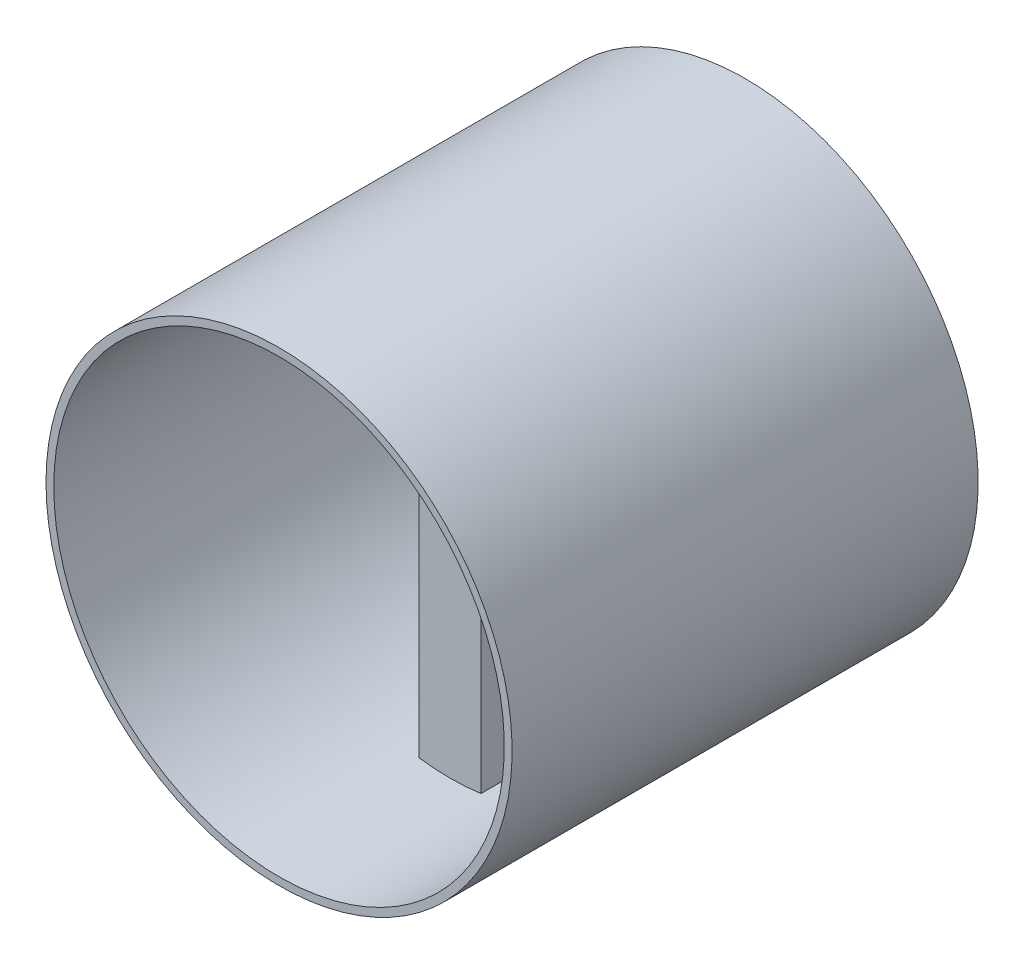
SolidWorks part; units mm, degrees
ref_plane "Plan de face" through (0, 0, 0) normal (0, 0, 1) x (1, 0, 0)
ref_plane "Plan de dessus" through (0, 0, 0) normal (0, 1, 0) x (1, 0, 0)
ref_plane "Plan de droite" through (0, 0, 0) normal (1, 0, 0) x (0, 0, -1)
sketch "Esquisse1" plane through (0, 0, 0) normal (0, 0, 1) x (1, 0, 0)
  line L1 (0, 0) -> (8, 0)
  line L2 (0, 0) -> (0, 59)
  line L3 (0, 59) -> (8, 59)
  line L4 (8, 0) -> (8, 59)
  dimension "D1" = 59
  dimension "D2" = 8
extrude "Boss.-Extru.1" add sketch "Esquisse1" along normal blind 60
sketch "Esquisse3" plane through (0, 0, 0) normal (0, 0, -1) x (-1, 0, 0)
  line L0 (-4, 59) -> (-4, 0) construction
  line L1 (-8, 59) -> (0, 59) construction
  line L2 (0, 0) -> (-8, 0) construction
  line L3 (0, 29.5) -> (-8, 29.5) construction
  line L4 (0, 59) -> (0, 0) construction
  line L5 (-8, 0) -> (-8, 59) construction
  circle A0 centre (-4, 29.5) radius 30
  circle A1 centre (-4, 29.5) radius 29
  dimension "D1" = 60
  dimension "D2" = 58
extrude "Boss.-Extru.2" add sketch "Esquisse3" against normal blind 60
sketch "Esquisse4" plane through (0, 0, 0) normal (0, 0, -1) x (-1, 0, 0)
  line L0 (-4, -0.5) -> (-4, 59.5) construction
  line L1 (-43.5151, 29.5) -> (32.2355, 29.5) construction
  circle A0 centre (-4, 29.5) radius 30 construction
  circle A5 centre (-4, 29.5) radius 29
  dimension "D1" = 58
extrude "Enlèv. mat.-Extru.3" cut sketch "Esquisse4" against normal blind 30
sketch "Esquisse5" plane through (0, 0, 30) normal (0, 0, -1) x (-1, 0, 0)
  line L0 (-4, 58.5) -> (-4, 0.5) construction
  line L1 (25, 29.5) -> (-33, 29.5) construction
  line L3 (-6, 43) -> (-6.9673, 29.942)
  line L5 (-6, 16) -> (-6.9673, 29.058)
  line L6 (-1.0327, 29.942) -> (-2, 43)
  line L7 (-2, 16) -> (-1.0327, 29.058)
  arc A0 (0, 58.2228) -> (-8, 58.2228) centre (-4, 29.5) ccw construction
  arc A1 (-8, 0.7772) -> (0, 0.7772) centre (-4, 29.5) ccw construction
  circle A2 centre (-4, 29.5) radius 29 construction
  arc A3 (-6.9673, 29.942) -> (-6.9673, 29.058) centre (-4, 29.5) ccw
  arc A4 (-2, 43) -> (-6, 43) centre (-4, 43) ccw
  arc A5 (-2, 16) -> (-6, 16) centre (-4, 16) cw
  arc A7 (-1.0327, 29.942) -> (-1.0327, 29.058) centre (-4, 29.5) cw
  dimension "D1" = 6
  dimension "D2" = 4
  dimension "D3" = 13.5
  dimension "D4" = 13.058
  dimension "D5" = 13.058
  dimension "D6" = 171.527
extrude "Enlèv. mat.-Extru.5" cut sketch "Esquisse5" against normal blind 1.5
sketch "Esquisse6" plane through (0, 0, 60) normal (0, 0, 1) x (1, 0, 0)
  line L0 (4, 59.5) -> (4, -0.5) construction
  line L1 (-25, 29.5) -> (33, 29.5) construction
  circle A0 centre (4, 29.5) radius 30 construction
  arc A1 (0, 58.2228) -> (0, 0.7772) centre (4, 29.5) ccw construction
  arc A2 (8, 0.7772) -> (8, 58.2228) centre (4, 29.5) ccw construction
  circle A3 centre (4, 29.5) radius 29
  dimension "D1" = 58
extrude "Enlèv. mat.-Extru.6" cut sketch "Esquisse6" against normal blind 22
sketch "Esquisse7" plane through (0, 0, 31.5) normal (0, 0, -1) x (-1, 0, 0)
  line L0 (-4, 45) -> (-4, 14) construction
  line L1 (-4, 14) -> (-33, 29.5) construction
  line L2 (-33, 29.5) -> (25, 29.5) construction
  arc A0 (-2, 43) -> (-6, 43) centre (-4, 43) ccw construction
  arc A1 (-6, 16) -> (-2, 16) centre (-4, 16) ccw construction
  circle A2 centre (-4, 29.5) radius 29 construction
  circle A3 centre (-4, 29.5) radius 2
  dimension "D1" = 4
extrude "Enlèv. mat.-Extru.7" cut sketch "Esquisse7" against normal blind 6.5
sketch "Esquisse8" plane through (0, 0, 31.5) normal (0, 0, -1) x (-1, 0, 0)
  line L0 (-4, 45) -> (-4, 14) construction
  line L1 (-33, 29.5) -> (25, 29.5) construction
  arc A0 (-2, 43) -> (-6, 43) centre (-4, 43) ccw construction
  arc A1 (-6, 16) -> (-2, 16) centre (-4, 16) ccw construction
  circle A2 centre (-4, 29.5) radius 29 construction
sketch "Esquisse9" plane through (0, 0, 38) normal (0, 0, 1) x (1, 0, 0)
  line L0 (4, 45) -> (4, 14) construction
  circle A0 centre (4, 29.5) radius 2
  dimension "D1" = 4
extrude "Boss.-Extru.4" add sketch "Esquisse9" against normal blind 6.5
sketch "Esquisse10" plane through (0, 0, 38) normal (0, 0, 1) x (1, 0, 0)
  line L0 (4, 45) -> (4, 14) construction
  circle A0 centre (4, 29.5) radius 2
  dimension "D1" = 4
extrude "Enlèv. mat.-Extru.8" cut sketch "Esquisse10" against normal blind 3.7
sketch "Esquisse11" plane through (0, 0, 34.3) normal (0, 0, 1) x (1, 0, 0)
  line L0 (4, 45) -> (4, 14) construction
  circle A0 centre (4, 29.5) radius 0.75
  dimension "D1" = 1.5
extrude "Enlèv. mat.-Extru.9" cut sketch "Esquisse11" against normal blind 3.7
